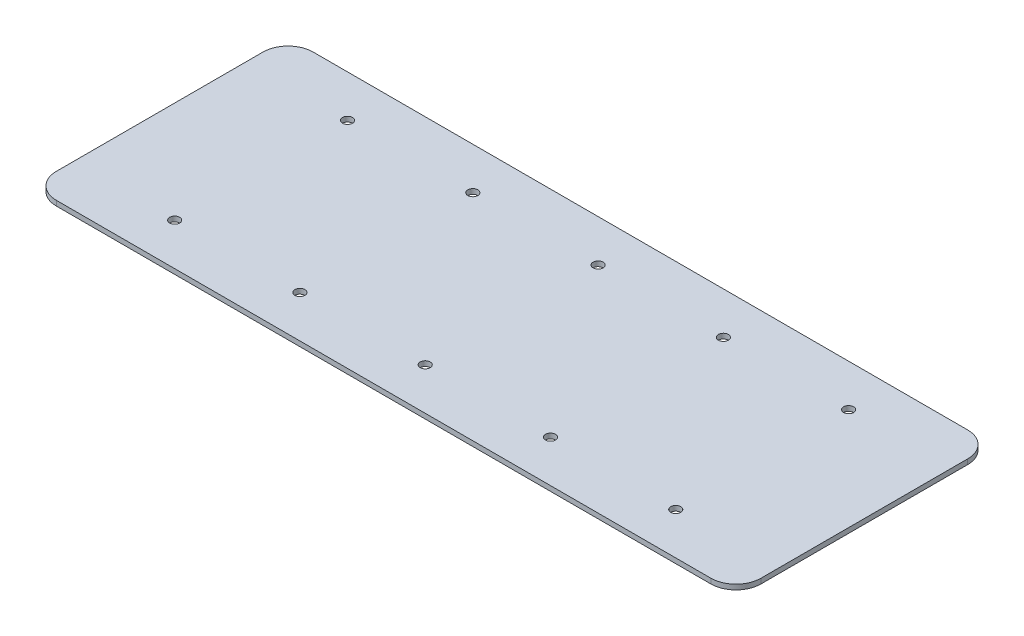
SolidWorks part; units mm, degrees
ref_plane "Front Plane" through (0, 0, 0) normal (0, 0, 1) x (1, 0, 0)
ref_plane "Top Plane" through (0, 0, 0) normal (0, 1, 0) x (1, 0, 0)
ref_plane "Right Plane" through (0, 0, 0) normal (1, 0, 0) x (0, 0, -1)
sketch "Sketch1" plane through (0, 0, 0) normal (0, 1, 0) x (1, 0, 0)
  line L1 (-112.5, -41) -> (112.5, -41)
  line L2 (-112.5, -41) -> (-112.5, 41)
  line L3 (-112.5, 41) -> (112.5, 41)
  line L4 (112.5, -41) -> (112.5, 41)
  line L5 (-112.5, -41) -> (112.5, 41) construction
  line L6 (-112.5, 41) -> (112.5, -41) construction
  point P0 (0, 0)
  dimension "D1" = 225
  dimension "D2" = 82
extrude "Boss-Extrude1" add sketch "Sketch1" along normal blind 1.6
fillet "Fillet1" radius 8 4 edges at (112.5, 0.8, -41) (112.5, 0.8, 41) (-112.5, 0.8, -41) (-112.5, 0.8, 41)
sketch "Sketch2" plane through (0, 1.6, 0) normal (0, 1, 0) x (1, 0, 0)
  circle A0 centre (-80.11, 27.6) radius 1.6
  circle A1 centre (-80.11, -27.6) radius 1.6
  circle A5 centre (-40.11, 27.6) radius 1.6
  circle A7 centre (-0.11, 27.6) radius 1.6
  circle A9 centre (39.89, 27.6) radius 1.6
  circle A11 centre (-40.11, -27.6) radius 1.6
  circle A13 centre (-0.11, -27.6) radius 1.6
  circle A15 centre (39.89, -27.6) radius 1.6
  circle A17 centre (79.89, -27.6) radius 1.6
  circle A19 centre (79.89, 27.6) radius 1.6
  dimension "D1" = 3.2
extrude "Cut-Extrude1" cut sketch "Sketch2" against normal through all both and the other way through all
